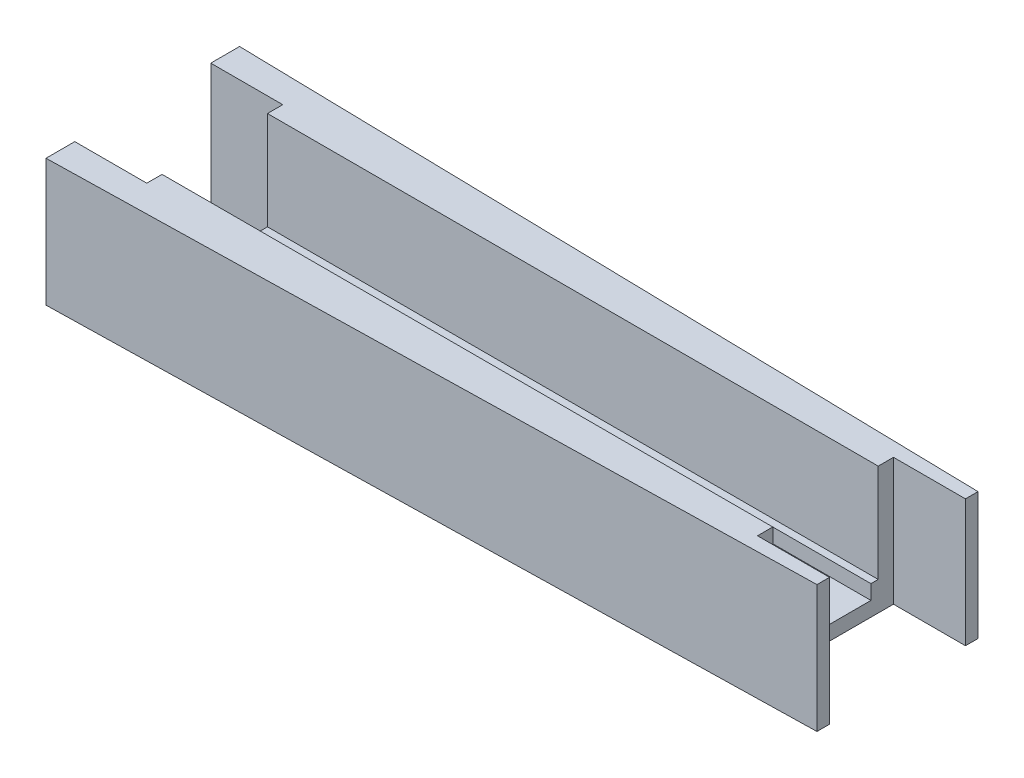
SolidWorks part; units mm, degrees
ref_plane "Front Plane" through (0, 0, 0) normal (0, 0, 1) x (1, 0, 0)
ref_plane "Top Plane" through (0, 0, 0) normal (0, 1, 0) x (1, 0, 0)
ref_plane "Right Plane" through (0, 0, 0) normal (1, 0, 0) x (0, 0, -1)
sketch "Sketch1" plane through (0, 0, 0) normal (0, 1, 0) x (1, 0, 0)
  line L0 (0.323, 14.9965) -> (267.1992, 9.2479)
  line L2 (267.1992, -9.2479) -> (0.323, -14.9965)
  arc A0 (0.323, 14.9965) -> (0.323, -14.9965) centre (0, 0) ccw
  arc A1 (267.1992, -9.2479) -> (267.1992, 9.2479) centre (267, 0) ccw
  dimension "D1" = 30
  dimension "D2" = 9.25
  dimension "D3" = 267
extrude "Boss-Extrude1" add sketch "Sketch1" along normal blind 17.5
sketch "Sketch2" plane through (0, 17.5, 0) normal (0, 1, 0) x (1, 0, 0)
  line L1 (15, 7.25) -> (267, 7.25)
  line L2 (15, 7.25) -> (15, -7.25)
  line L3 (15, -7.25) -> (267, -7.25)
  line L4 (267, 7.25) -> (267, -7.25)
  line L5 (15, 7.25) -> (267, -7.25) construction
  line L6 (15, -7.25) -> (267, 7.25) construction
  circle A0 centre (0, 0) radius 15 construction
  arc A1 (0.323, 14.9965) -> (0.323, -14.9965) centre (0, 0) ccw construction
  point P0 (141, 0)
  dimension "D1" = 252
  dimension "D2" = 14.5
extrude "Cut-Extrude1" cut sketch "Sketch2" against normal blind 15.5
sketch "Sketch3" plane through (0, 17.5, 0) normal (0, 1, 0) x (1, 0, 0)
  circle A0 centre (0, 0) radius 13
  dimension "D1" = 26
extrude "Cut-Extrude2" cut sketch "Sketch3" against normal blind 15.5
sketch "Sketch4" plane through (15, 0, 0) normal (1, 0, 0) x (0, 0, -1)
  line L0 (7.25, 2) -> (7.25, 17.5) construction
  line L1 (-7.25, 2) -> (7.25, 2)
  line L2 (-7.25, 2) -> (-7.25, 8.5)
  line L3 (-0.25, 15.5) -> (0.25, 15.5)
  line L4 (7.25, 2) -> (7.25, 8.5)
  line L5 (7.25, 17.5) -> (-7.25, 17.5) construction
  arc A0 (7.25, 8.5) -> (0.25, 15.5) centre (0.25, 8.5) ccw
  arc A1 (-7.25, 8.5) -> (-0.25, 15.5) centre (-0.25, 8.5) cw
  point P11 (7.25, 15.5)
  dimension "D2" = 7
  dimension "D1" = 2
extrude "Cut-Extrude3" cut sketch "Sketch4" against normal up to surface (4.2094 mm away)
sketch "Sketch5" plane through (0, 2, 0) normal (0, 1, 0) x (1, 0, 0)
  line L0 (267, -7.25) -> (267, 7.25) construction
  line L1 (15, 7.25) -> (267, 7.25)
  line L2 (15, 7.25) -> (15, 6.25)
  line L3 (15, 6.25) -> (267, 6.25)
  line L4 (267, 7.25) -> (267, 6.25)
  line L5 (15, 7.25) -> (15, -7.25) construction
  line L10 (267, -7.25) -> (15, -7.25)
  line L11 (267, -7.25) -> (267, -6.25)
  line L12 (267, -6.25) -> (15, -6.25)
  line L13 (15, -7.25) -> (15, -6.25)
  dimension "D1" = 1
  dimension "D2" = 1
extrude "Boss-Extrude2" add sketch "Sketch5" along normal blind 2
sketch "Sketch6" plane through (0, 2, 0) normal (0, 1, 0) x (1, 0, 0)
  line L1 (0, -10) -> (8.6603, -5)
  line L2 (8.6603, -5) -> (8.6603, 5)
  line L3 (8.6603, 5) -> (0, 10)
  line L4 (0, 10) -> (-8.6603, 5)
  line L5 (-8.6603, 5) -> (-8.6603, -5)
  line L6 (-8.6603, -5) -> (0, -10)
  line L7 (-5.25, 9.0933) -> (-10.5, 0) construction
  line L8 (-10.5, 0) -> (-5.25, -9.0933) construction
  line L9 (-5.25, -9.0933) -> (5.25, -9.0933) construction
  line L10 (5.25, -9.0933) -> (10.5, 0) construction
  line L11 (10.5, 0) -> (5.25, 9.0933) construction
  line L12 (5.25, 9.0933) -> (-5.25, 9.0933) construction
  circle A1 centre (0, 0) radius 8.6603 construction
  circle A2 centre (0, 0) radius 9.0933 construction
  circle A3 centre (-5.25, 9.0933) radius 1
  circle A4 centre (-10.5, 0) radius 1
  circle A5 centre (5.25, 9.0933) radius 1
  circle A6 centre (10.5, 0) radius 1
  circle A7 centre (5.25, -9.0933) radius 1
  circle A8 centre (-5.25, -9.0933) radius 1
  dimension "D1" = 2
  dimension "D2" = 20
  dimension "D3" = 21
extrude "Cut-Extrude4" cut sketch "Sketch6" against normal up to surface (2 mm away) up to face at (132.1931, 0, 0)
sketch "Sketch14" plane through (0, 0, 0) normal (0, 1, 0) x (1, 0, 0)
  line L0 (-15, -35) -> (-15, 35) construction
  line L1 (88.5, 35) -> (88.5, -35) construction
  line L2 (276.25, 35) -> (276.25, -35) construction
  line L3 (-15, -35) -> (276.25, -35) construction
  line L4 (-15, 35) -> (276.25, 35) construction
  line L5 (172.5, 35) -> (172.5, -35) construction
  line L6 (88.5, 9.25) -> (78.5, 9.25) construction
  line L7 (78.5, 9.25) -> (78.5, 35) construction
  line L8 (0, 0) -> (276.25, 0) construction
  line L9 (172.5, 9.25) -> (182.5, 9.25) construction
  line L10 (182.5, 9.25) -> (182.5, 35) construction
  line L11 (267, 7.25) -> (15, 7.25) construction
  line L12 (267, 7.25) -> (15, 7.25) construction
  line L13 (88.5, 9.35) -> (78.6, 9.35)
  line L14 (78.6, 9.35) -> (78.6, 35)
  line L15 (88.3, 9.15) -> (78.4, 9.15)
  line L16 (78.4, 9.15) -> (78.4, 35)
  line L17 (172.7, 9.15) -> (182.6, 9.15)
  line L18 (182.6, 9.15) -> (182.6, 35)
  line L19 (172.5, 9.35) -> (182.4, 9.35)
  line L20 (182.4, 9.35) -> (182.4, 35)
  line L21 (78.4, 35) -> (78.6, 35)
  line L22 (182.4, 35) -> (182.6, 35)
  line L23 (88.5, -9.35) -> (78.6, -9.35)
  line L24 (88.3, -9.15) -> (78.4, -9.15)
  line L25 (88.5, 9.15) -> (78.4, 9.15) construction
  line L26 (172.5, 9.15) -> (182.6, 9.15) construction
  line L27 (78.6, -9.35) -> (78.6, -35)
  line L28 (78.4, -9.15) -> (78.4, -35)
  line L29 (78.4, -35) -> (78.6, -35)
  line L30 (182.4, -35) -> (182.6, -35)
  line L31 (182.4, -9.35) -> (182.4, -35)
  line L32 (182.6, -9.15) -> (182.6, -35)
  line L33 (172.7, -9.15) -> (182.6, -9.15)
  line L34 (172.5, -9.35) -> (182.4, -9.35)
  line L35 (88.5, 9.35) -> (88.5, -9.35)
  line L36 (88.3, -9.15) -> (88.3, 9.15)
  line L37 (172.5, 9.25) -> (172.5, -9.35)
  line L38 (172.7, -9.15) -> (172.7, 9.15)
  line L39 (172.5, 9.35) -> (172.5, 9.25)
  arc A0 (0.323, 14.9965) -> (0.323, -14.9965) centre (0, 0) ccw construction
  arc A1 (267.1992, -9.2479) -> (267.1992, 9.2479) centre (267, 0) ccw construction
  point P8 (276.25, 0)
  point P9 (-15, 0)
  dimension "D1" = 103.5
  dimension "D2" = 84
  dimension "D3" = 70
  dimension "D4" = 2
  dimension "D5" = 2
  dimension "D6" = 10
  dimension "D7" = 10
  dimension "D12" = 0.2
  dimension "D13" = 0.2
  dimension "D8" = 0.1
  dimension "D9" = 0.1
  dimension "D10" = 0.1
  dimension "D11" = 0.1
extrude "Cut-Extrude9" cut sketch "Sketch14" along normal through all
